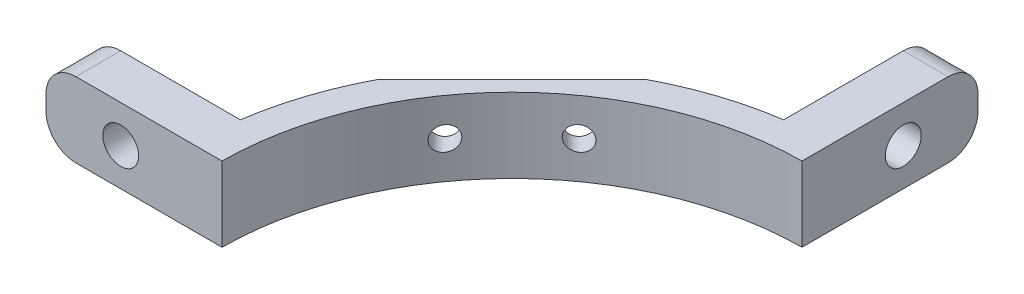
SolidWorks part; units mm, degrees
material "6061-T6 (SS)"
ref_plane "Front Plane" through (0, 0, 0) normal (0, 0, 1) x (1, 0, 0)
ref_plane "Top Plane" through (0, 0, 0) normal (0, 1, 0) x (1, 0, 0)
ref_plane "Right Plane" through (0, 0, 0) normal (1, 0, 0) x (0, 0, -1)
sketch "Sketch1" plane through (0, 0, 0) normal (0, 1, 0) x (1, 0, 0)
  line L0 (-3.1, 31.2753) -> (-3.1, 21.2753)
  line L1 (-0.1, 31.2753) -> (-0.1, 19.4997)
  line L2 (-0.1, 31.2753) -> (-3.1, 31.2753)
  line L3 (-21.2753, 3.1) -> (-31.2753, 3.1)
  line L4 (-31.2753, 3.1) -> (-31.2753, 0.1)
  line L5 (-31.2753, 0.1) -> (-19.4997, 0.1)
  arc A0 (-0.1, 19.4997) -> (-19.4997, 0.1) centre (0, 0) ccw
  arc A1 (-3.1, 21.2753) -> (-21.2753, 3.1) centre (0, 0) ccw
  dimension "D1" = 39
  dimension "D2" = 43
  dimension "D3" = 3
  dimension "D4" = 10
  dimension "D5" = 0.1
  dimension "D6" = 0.1
extrude "Boss-Extrude1" add sketch "Sketch1" along normal mid plane 5
sketch3d "3DSketch2"
  line L0 (-21.2753, -2.5, -3.1) -> (-31.2753, -2.5, -3.1) construction
  line L1 (-31.2753, 2.5, -3.1) -> (-31.2753, -2.5, -3.1) construction
  line L4 (-0.1, 2.5, -31.2753) -> (-0.1, -2.5, -31.2753) construction
  line L5 (-3.1, -2.5, -26.2753) -> (-0.1, -2.5, -26.2753) construction
  line L6 (-3.1, -2.5, -31.2753) -> (-3.1, -2.5, -21.2753) construction
  line L7 (-0.1, -2.5, -19.4997) -> (-0.1, -2.5, -31.2753) construction
  point P1 (-26.2753, 0, -3.1)
  point P4 (-26.2753, -2.5, -3.1)
  point P7 (-31.2753, 0, -3.1)
  point P9 (-0.1, 0, -26.2753)
  point P16 (-0.1, 0, -31.2753)
hole_wizard "M2 Clearance Hole1" positions "3DSketch5" profile "Sketch8" hole size "M2" standard "ANSI Metric"
sketch3d "3DSketch5"
  point P0 (-26.2753, 0, -3.1)
  point P3 (-26.2753, 0, -3.1)
  point P13 (-0.1, 0, -26.2753)
sketch "Sketch8" plane through (-0.1, 0, -26.2753) normal (0, 1, 0) x (0, 0, -1)
  line L0 (0, 0) -> (0, 31.1753)
  line L1 (0, 31.1753) -> (1.2, 31.1753)
  line L2 (1.2, 31.1753) -> (1.2, 0)
  line L5 (1.2, 0) -> (0, 0)
  line L11 (0, -6.35) -> (0, 107.95) construction
  dimension "Thru Hole Dia." = 2.4
  dimension "Thru Hole Depth" = 31.1753
fillet "Fillet1" radius 2 4 edges at (-31.2753, 2.5, -1.6) (-31.2753, -2.5, -1.6) (-1.6, 2.5, -31.2753) (-1.6, -2.5, -31.2753)
sketch "Sketch9" plane through (0, 2.5, 0) normal (0, 1, 0) x (1, 0, 0)
  line L2 (-29.2753, 0.1) -> (-19.4997, 0.1) construction
  line L4 (-21.2753, 3.1) -> (-29.2753, 3.1) construction
  line L6 (-0.1, 19.4997) -> (-0.1, 29.2753) construction
  line L7 (-3.1, 29.2753) -> (-3.1, 21.2753) construction
  line L8 (-26.2753, 0.1) -> (-21.4998, 0.1)
  line L9 (-26.2753, 3.1) -> (-26.2753, 0.1)
  line L10 (-21.2753, 3.1) -> (-26.2753, 3.1)
  line L11 (-0.1, 26.2753) -> (-3.1, 26.2753)
  line L12 (-0.1, 21.4998) -> (-0.1, 26.2753)
  line L13 (-3.1, 26.2753) -> (-3.1, 21.2753)
  line L17 (-29.2753, 3.1) -> (-29.2753, 0.1) construction
  line L18 (-0.1, 29.2753) -> (-3.1, 29.2753) construction
  arc A9 (-21.4998, 0.1) -> (-21.2753, 3.1) centre (0, 0) cw
  arc A10 (-3.1, 21.2753) -> (-21.2753, 3.1) centre (0, 0) ccw construction
  arc A11 (-3.1, 21.2753) -> (-0.1, 21.4998) centre (0, 0) cw
  dimension "D1" = 5
  dimension "D2" = 5
extrude "Boss-Extrude2" [suppressed] add sketch "Sketch9" along normal blind 29.95
sketch "Sketch10" [suppressed] plane through (0, 33.45, 0) normal (0, 1, 0) x (1, 0, 0)
  line L0 (-29.7805, 3.1) -> (-29.7805, 8.1)
  line L1 (-29.7805, 8.1) -> (-17.7381, 8.1)
  line L2 (-19.252, 3.1) -> (-29.7805, 3.1) construction
  line L3 (-19.252, 3.1) -> (-29.7805, 3.1)
  line L4 (-3.1, 29.7805) -> (-3.1, 19.252) construction
  line L5 (-3.1, 29.7805) -> (-3.1, 19.252)
  line L6 (-3.1, 29.7805) -> (-8.1, 29.7805)
  line L7 (-8.1, 29.7805) -> (-8.1, 17.7381)
  arc A0 (-3.1, 19.252) -> (-19.252, 3.1) centre (0, 0) ccw construction
  arc A1 (-3.1, 19.252) -> (-8.1, 17.7381) centre (0, 0) ccw
  arc A2 (-17.7381, 8.1) -> (-19.252, 3.1) centre (0, 0) ccw
  dimension "D1" = 5
  dimension "D2" = 5
extrude "Boss-Extrude3" [suppressed] add sketch "Sketch10" against normal blind 3
sketch "Sketch11" plane through (0, -2.5, 0) normal (0, -1, 0) x (1, 0, 0)
  line L0 (-19.0147, -10.0345) -> (-10.0345, -19.0147)
  line L1 (-10.0345, -19.0147) -> (-10.7127, -19.6929)
  line L2 (-10.7127, -19.6929) -> (-19.6929, -10.7127)
  line L3 (-19.6929, -10.7127) -> (-19.0147, -10.0345)
  line L4 (-14.5246, -14.5246) -> (-15.2028, -15.2028) construction
  arc A0 (-21.2753, -3.1) -> (-3.1, -21.2753) centre (0, 0) ccw construction
  point P8 (-15.2028, -15.2028)
  dimension "D1" = 12.7
extrude "Cut-Extrude1" cut sketch "Sketch11" against normal through all
sketch "Sketch12" plane through (-14.5246, 0, -14.5246) normal (-0.7071, 0, -0.7071) x (-0.7071, 0, 0.7071)
  line L0 (0, -2.5) -> (0, 2.5) construction
  line L1 (-6.35, -2.5) -> (6.35, -2.5) construction
  line L2 (-6.35, 2.5) -> (6.35, 2.5) construction
  line L3 (0, 0) -> (6.35, 0) construction
  line L4 (6.35, 2.5) -> (6.35, -2.5) construction
  point P0 (3.175, 0)
  point P11 (0, 0)
  point P12 (-3.175, 0)
hole_wizard "M2x0.4 Tapped Hole1" positions "Sketch13" profile "Sketch14" tap size "M2x0.4" standard "ANSI Metric"
sketch "Sketch13" plane through (-14.5246, 0, -14.5246) normal (-0.7071, 0, -0.7071) x (-0.7071, 0, 0.7071)
  point P0 (3.175, 0)
  point P3 (-3.175, 0)
sketch "Sketch14" plane through (-16.7697, 0, -12.2795) normal (0, 1, 0) x (-0.7071, 0, 0.7071)
  line L0 (0, 0) -> (0, 20.3995)
  line L1 (0, 20.3995) -> (0.8, 20.3995)
  line L2 (0.8, 20.3995) -> (0.8, 0)
  line L5 (0.8, 0) -> (0, 0)
  line L11 (0, -6.35) -> (0, 107.95) construction
  dimension "Thru Tap Drill Dia." = 1.6
  dimension "Thru Tap Drill Depth" = 20.3995
cosmetic thread "Hole Thread1" parameters "D2"=2
cosmetic thread "Hole Thread2" parameters "D2"=2
